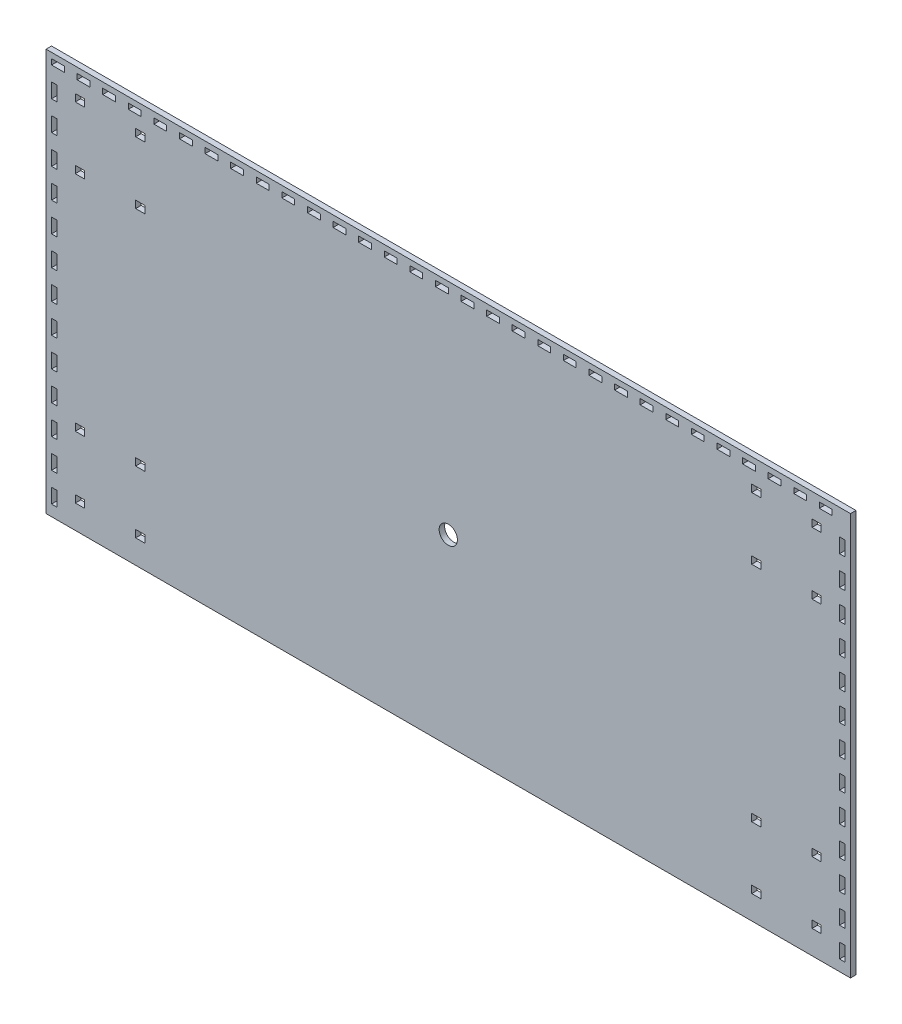
SolidWorks part; units mm, degrees
ref_plane "Plan de face" through (0, 0, 0) normal (0, 0, 1) x (1, 0, 0)
ref_plane "Plan de dessus" through (0, 0, 0) normal (0, 1, 0) x (1, 0, 0)
ref_plane "Plan de droite" through (0, 0, 0) normal (1, 0, 0) x (0, 0, -1)
sketch "Esquisse1" plane through (0, 0, 0) normal (0, 0, 1) x (1, 0, 0)
  line L1 (-220, 110) -> (220, 110)
  line L2 (-220, 110) -> (-220, -110)
  line L3 (-220, -110) -> (220, -110)
  line L4 (220, 110) -> (220, -110)
  line L5 (-220, 110) -> (220, -110) construction
  line L6 (-220, -110) -> (220, 110) construction
  point P0 (0, 0)
  dimension "D1" = 440
  dimension "D2" = 220
extrude "Boss.-Extru.1" add sketch "Esquisse1" along normal blind 3
sketch "Esquisse2" plane through (0, 0, 3) normal (0, 0, 1) x (1, 0, 0)
  line L0 (-220, -10) -> (220, -10) construction
  line L1 (-220, 110) -> (-220, -110) construction
  line L2 (220, -110) -> (220, 110) construction
  line L3 (0, 110) -> (0, -110) construction
  line L4 (220, 110) -> (-220, 110) construction
  line L5 (-220, -110) -> (220, -110) construction
  circle A0 centre (0, -10) radius 5
  dimension "D2" = 10
  dimension "D1" = 100
extrude "Enlèv. mat.-Extru.1" cut sketch "Esquisse2" against normal blind 3
sketch "Esquisse3" plane through (0, 0, 3) normal (0, 0, 1) x (1, 0, 0)
  line L0 (-185, 94) -> (-185, 62) construction
  line L1 (-201, 78) -> (-169, 78) construction
  line L2 (-220, 110) -> (-220, -110) construction
  line L3 (220, 110) -> (-220, 110) construction
  line L4 (-171, 95) -> (-199, 95) construction
  line L5 (-204, 97) -> (-199, 97)
  line L6 (-204, 97) -> (-204, 93)
  line L7 (-204, 93) -> (-199, 93)
  line L8 (-199, 97) -> (-199, 93)
  line L9 (-204, 97) -> (-199, 93) construction
  line L10 (-204, 93) -> (-199, 97) construction
  line L11 (-166, 97) -> (-171, 97)
  line L12 (-166, 97) -> (-166, 93)
  line L13 (-166, 93) -> (-171, 93)
  line L14 (-171, 97) -> (-171, 93)
  line L15 (-166, 97) -> (-171, 93) construction
  line L16 (-166, 93) -> (-171, 97) construction
  line L17 (-166, 63) -> (-171, 63)
  line L18 (-166, 59) -> (-166, 63)
  line L19 (-166, 59) -> (-171, 59)
  line L20 (-171, 59) -> (-171, 63)
  line L21 (-199, 59) -> (-199, 63)
  line L22 (-204, 63) -> (-199, 63)
  line L23 (-204, 59) -> (-204, 63)
  line L24 (-204, 59) -> (-199, 59)
  line L25 (0, 110) -> (0, -110) construction
  line L26 (-220, -110) -> (220, -110) construction
  line L27 (-220, 0) -> (220, 0) construction
  line L28 (220, -110) -> (220, 110) construction
  line L29 (171, 59) -> (171, 63)
  line L30 (166, 59) -> (171, 59)
  line L31 (166, 59) -> (166, 63)
  line L32 (166, 63) -> (171, 63)
  line L33 (204, 59) -> (199, 59)
  line L34 (204, 59) -> (204, 63)
  line L35 (204, 63) -> (199, 63)
  line L36 (199, 59) -> (199, 63)
  line L37 (166, 93) -> (171, 93)
  line L38 (166, 97) -> (166, 93)
  line L39 (166, 97) -> (171, 97)
  line L40 (171, 97) -> (171, 93)
  line L41 (199, 97) -> (199, 93)
  line L42 (204, 93) -> (199, 93)
  line L43 (204, 97) -> (204, 93)
  line L44 (204, 97) -> (199, 97)
  line L45 (-166, -97) -> (-166, -93)
  line L46 (-166, -93) -> (-171, -93)
  line L47 (-171, -97) -> (-171, -93)
  line L48 (-166, -97) -> (-171, -97)
  line L49 (-204, -93) -> (-199, -93)
  line L50 (-199, -97) -> (-199, -93)
  line L51 (-204, -97) -> (-199, -97)
  line L52 (-204, -97) -> (-204, -93)
  line L53 (-166, -63) -> (-171, -63)
  line L54 (-171, -59) -> (-171, -63)
  line L55 (-166, -59) -> (-171, -59)
  line L56 (-166, -59) -> (-166, -63)
  line L57 (-204, -59) -> (-199, -59)
  line L58 (-204, -59) -> (-204, -63)
  line L59 (-204, -63) -> (-199, -63)
  line L60 (-199, -59) -> (-199, -63)
  line L61 (204, -97) -> (199, -97)
  line L62 (204, -97) -> (204, -93)
  line L63 (204, -93) -> (199, -93)
  line L64 (199, -97) -> (199, -93)
  line L65 (171, -97) -> (171, -93)
  line L66 (166, -97) -> (171, -97)
  line L67 (166, -97) -> (166, -93)
  line L68 (166, -93) -> (171, -93)
  line L69 (199, -59) -> (199, -63)
  line L70 (204, -63) -> (199, -63)
  line L71 (204, -59) -> (204, -63)
  line L72 (204, -59) -> (199, -59)
  line L73 (166, -63) -> (171, -63)
  line L74 (166, -59) -> (166, -63)
  line L75 (166, -59) -> (171, -59)
  line L76 (171, -59) -> (171, -63)
  circle A0 centre (-185, 78) radius 16 construction
  point P10 (-201.5, 95)
  point P15 (-168.5, 95)
  dimension "D1" = 35
  dimension "D3" = 32
  dimension "D2" = 32
  dimension "D4" = 5
  dimension "D5" = 4
  dimension "D6" = 28
  dimension "D7" = 5
  dimension "D8" = 4
  dimension "D9" = 15
  dimension "D10" = 14
extrude "Enlèv. mat.-Extru.2" cut sketch "Esquisse3" against normal blind 3
sketch "Esquisse4" plane through (0, 0, 3) normal (0, 0, 1) x (1, 0, 0)
  line L0 (220, 110) -> (-220, 110) construction
  line L1 (-217, 107) -> (-210, 107)
  line L2 (-217, 107) -> (-217, 104)
  line L3 (-217, 104) -> (-210, 104)
  line L4 (-210, 107) -> (-210, 104)
  line L5 (-220, 110) -> (-220, -110) construction
  line L6 (-203, 107) -> (-203, 104)
  line L7 (-203, 107) -> (-196, 107)
  line L8 (-196, 107) -> (-196, 104)
  line L9 (-203, 104) -> (-196, 104)
  line L10 (-189, 107) -> (-189, 104)
  line L11 (-189, 107) -> (-182, 107)
  line L12 (-182, 107) -> (-182, 104)
  line L13 (-189, 104) -> (-182, 104)
  line L14 (-175, 107) -> (-175, 104)
  line L15 (-175, 107) -> (-168, 107)
  line L16 (-168, 107) -> (-168, 104)
  line L17 (-175, 104) -> (-168, 104)
  line L18 (-161, 107) -> (-161, 104)
  line L19 (-161, 107) -> (-154, 107)
  line L20 (-154, 107) -> (-154, 104)
  line L21 (-161, 104) -> (-154, 104)
  line L22 (-147, 107) -> (-147, 104)
  line L23 (-147, 107) -> (-140, 107)
  line L24 (-140, 107) -> (-140, 104)
  line L25 (-147, 104) -> (-140, 104)
  line L26 (-133, 107) -> (-133, 104)
  line L27 (-133, 107) -> (-126, 107)
  line L28 (-126, 107) -> (-126, 104)
  line L29 (-133, 104) -> (-126, 104)
  line L30 (-119, 107) -> (-119, 104)
  line L31 (-119, 107) -> (-112, 107)
  line L32 (-112, 107) -> (-112, 104)
  line L33 (-119, 104) -> (-112, 104)
  line L34 (-105, 107) -> (-105, 104)
  line L35 (-105, 107) -> (-98, 107)
  line L36 (-98, 107) -> (-98, 104)
  line L37 (-105, 104) -> (-98, 104)
  line L38 (-91, 107) -> (-91, 104)
  line L39 (-91, 107) -> (-84, 107)
  line L40 (-84, 107) -> (-84, 104)
  line L41 (-91, 104) -> (-84, 104)
  line L42 (-77, 107) -> (-77, 104)
  line L43 (-77, 107) -> (-70, 107)
  line L44 (-70, 107) -> (-70, 104)
  line L45 (-77, 104) -> (-70, 104)
  line L46 (-63, 107) -> (-63, 104)
  line L47 (-63, 107) -> (-56, 107)
  line L48 (-56, 107) -> (-56, 104)
  line L49 (-63, 104) -> (-56, 104)
  line L50 (-49, 107) -> (-49, 104)
  line L51 (-49, 107) -> (-42, 107)
  line L52 (-42, 107) -> (-42, 104)
  line L53 (-49, 104) -> (-42, 104)
  line L54 (-35, 107) -> (-35, 104)
  line L55 (-35, 107) -> (-28, 107)
  line L56 (-28, 107) -> (-28, 104)
  line L57 (-35, 104) -> (-28, 104)
  line L58 (-21, 107) -> (-21, 104)
  line L59 (-21, 107) -> (-14, 107)
  line L60 (-14, 107) -> (-14, 104)
  line L61 (-21, 104) -> (-14, 104)
  line L62 (-7, 107) -> (-7, 104)
  line L63 (-7, 107) -> (0, 107)
  line L64 (0, 107) -> (0, 104)
  line L65 (-7, 104) -> (0, 104)
  line L66 (7, 107) -> (7, 104)
  line L67 (7, 107) -> (14, 107)
  line L68 (14, 107) -> (14, 104)
  line L69 (7, 104) -> (14, 104)
  line L70 (21, 107) -> (21, 104)
  line L71 (21, 107) -> (28, 107)
  line L72 (28, 107) -> (28, 104)
  line L73 (21, 104) -> (28, 104)
  line L74 (35, 107) -> (35, 104)
  line L75 (35, 107) -> (42, 107)
  line L76 (42, 107) -> (42, 104)
  line L77 (35, 104) -> (42, 104)
  line L78 (49, 107) -> (49, 104)
  line L79 (49, 107) -> (56, 107)
  line L80 (56, 107) -> (56, 104)
  line L81 (49, 104) -> (56, 104)
  line L82 (63, 107) -> (63, 104)
  line L83 (63, 107) -> (70, 107)
  line L84 (70, 107) -> (70, 104)
  line L85 (63, 104) -> (70, 104)
  line L86 (77, 107) -> (77, 104)
  line L87 (77, 107) -> (84, 107)
  line L88 (84, 107) -> (84, 104)
  line L89 (77, 104) -> (84, 104)
  line L90 (91, 107) -> (91, 104)
  line L91 (91, 107) -> (98, 107)
  line L92 (98, 107) -> (98, 104)
  line L93 (91, 104) -> (98, 104)
  line L94 (105, 107) -> (105, 104)
  line L95 (105, 107) -> (112, 107)
  line L96 (112, 107) -> (112, 104)
  line L97 (105, 104) -> (112, 104)
  line L98 (119, 107) -> (119, 104)
  line L99 (119, 107) -> (126, 107)
  line L100 (126, 107) -> (126, 104)
  line L101 (119, 104) -> (126, 104)
  line L102 (133, 107) -> (133, 104)
  line L103 (133, 107) -> (140, 107)
  line L104 (140, 107) -> (140, 104)
  line L105 (133, 104) -> (140, 104)
  line L106 (147, 107) -> (147, 104)
  line L107 (147, 107) -> (154, 107)
  line L108 (154, 107) -> (154, 104)
  line L109 (147, 104) -> (154, 104)
  line L110 (161, 107) -> (161, 104)
  line L111 (161, 107) -> (168, 107)
  line L112 (168, 107) -> (168, 104)
  line L113 (161, 104) -> (168, 104)
  line L114 (175, 107) -> (175, 104)
  line L115 (175, 107) -> (182, 107)
  line L116 (182, 107) -> (182, 104)
  line L117 (175, 104) -> (182, 104)
  line L118 (189, 107) -> (189, 104)
  line L119 (189, 107) -> (196, 107)
  line L120 (196, 107) -> (196, 104)
  line L121 (189, 104) -> (196, 104)
  line L122 (203, 107) -> (203, 104)
  line L123 (203, 107) -> (210, 107)
  line L124 (210, 107) -> (210, 104)
  line L125 (203, 104) -> (210, 104)
  dimension "D1" = 7
  dimension "D2" = 3
  dimension "D3" = 3
  dimension "D4" = 3
  dimension "D6" = 7
  dimension "D5" = 31
extrude "Enlèv. mat.-Extru.3" cut sketch "Esquisse4" against normal blind 3
sketch "Esquisse5" plane through (0, 0, 3) normal (0, 0, 1) x (1, 0, 0)
  line L0 (-220, -110) -> (220, -110) construction
  line L1 (-217, -104) -> (-214, -104)
  line L2 (-217, -104) -> (-217, -96)
  line L3 (-217, -96) -> (-214, -96)
  line L4 (-214, -104) -> (-214, -96)
  line L5 (-220, 110) -> (-220, -110) construction
  line L6 (-217, -80) -> (-214, -80)
  line L7 (-217, -88) -> (-217, -80)
  line L8 (-214, -88) -> (-214, -80)
  line L9 (-217, -88) -> (-214, -88)
  line L10 (-217, -64) -> (-214, -64)
  line L11 (-217, -72) -> (-217, -64)
  line L12 (-214, -72) -> (-214, -64)
  line L13 (-217, -72) -> (-214, -72)
  line L14 (-217, -48) -> (-214, -48)
  line L15 (-217, -56) -> (-217, -48)
  line L16 (-214, -56) -> (-214, -48)
  line L17 (-217, -56) -> (-214, -56)
  line L18 (-217, -32) -> (-214, -32)
  line L19 (-217, -40) -> (-217, -32)
  line L20 (-214, -40) -> (-214, -32)
  line L21 (-217, -40) -> (-214, -40)
  line L22 (-217, -16) -> (-214, -16)
  line L23 (-217, -24) -> (-217, -16)
  line L24 (-214, -24) -> (-214, -16)
  line L25 (-217, -24) -> (-214, -24)
  line L26 (-217, 0) -> (-214, 0)
  line L27 (-217, -8) -> (-217, 0)
  line L28 (-214, -8) -> (-214, 0)
  line L29 (-217, -8) -> (-214, -8)
  line L30 (-217, 16) -> (-214, 16)
  line L31 (-217, 8) -> (-217, 16)
  line L32 (-214, 8) -> (-214, 16)
  line L33 (-217, 8) -> (-214, 8)
  line L34 (-217, 32) -> (-214, 32)
  line L35 (-217, 24) -> (-217, 32)
  line L36 (-214, 24) -> (-214, 32)
  line L37 (-217, 24) -> (-214, 24)
  line L38 (-217, 48) -> (-214, 48)
  line L39 (-217, 40) -> (-217, 48)
  line L40 (-214, 40) -> (-214, 48)
  line L41 (-217, 40) -> (-214, 40)
  line L42 (-217, 64) -> (-214, 64)
  line L43 (-217, 56) -> (-217, 64)
  line L44 (-214, 56) -> (-214, 64)
  line L45 (-217, 56) -> (-214, 56)
  line L46 (-217, 80) -> (-214, 80)
  line L47 (-217, 72) -> (-217, 80)
  line L48 (-214, 72) -> (-214, 80)
  line L49 (-217, 72) -> (-214, 72)
  line L50 (-217, 96) -> (-214, 96)
  line L51 (-217, 88) -> (-217, 96)
  line L52 (-214, 88) -> (-214, 96)
  line L53 (-217, 88) -> (-214, 88)
  line L54 (0, 110) -> (0, -110) construction
  line L55 (220, 110) -> (-220, 110) construction
  line L56 (217, 88) -> (214, 88)
  line L57 (214, 88) -> (214, 96)
  line L58 (217, 88) -> (217, 96)
  line L59 (217, 96) -> (214, 96)
  line L60 (217, 72) -> (214, 72)
  line L61 (214, 72) -> (214, 80)
  line L62 (217, 72) -> (217, 80)
  line L63 (217, 80) -> (214, 80)
  line L64 (217, 56) -> (214, 56)
  line L65 (214, 56) -> (214, 64)
  line L66 (217, 56) -> (217, 64)
  line L67 (217, 64) -> (214, 64)
  line L68 (217, 40) -> (214, 40)
  line L69 (214, 40) -> (214, 48)
  line L70 (217, 40) -> (217, 48)
  line L71 (217, 48) -> (214, 48)
  line L72 (217, 24) -> (214, 24)
  line L73 (214, 24) -> (214, 32)
  line L74 (217, 24) -> (217, 32)
  line L75 (217, 32) -> (214, 32)
  line L76 (217, 8) -> (214, 8)
  line L77 (214, 8) -> (214, 16)
  line L78 (217, 8) -> (217, 16)
  line L79 (217, 16) -> (214, 16)
  line L80 (217, -8) -> (214, -8)
  line L81 (214, -8) -> (214, 0)
  line L82 (217, -8) -> (217, 0)
  line L83 (217, 0) -> (214, 0)
  line L84 (217, -24) -> (214, -24)
  line L85 (214, -24) -> (214, -16)
  line L86 (217, -24) -> (217, -16)
  line L87 (217, -16) -> (214, -16)
  line L88 (217, -40) -> (214, -40)
  line L89 (214, -40) -> (214, -32)
  line L90 (217, -40) -> (217, -32)
  line L91 (217, -32) -> (214, -32)
  line L92 (217, -56) -> (214, -56)
  line L93 (214, -56) -> (214, -48)
  line L94 (217, -56) -> (217, -48)
  line L95 (217, -48) -> (214, -48)
  line L96 (217, -72) -> (214, -72)
  line L97 (214, -72) -> (214, -64)
  line L98 (217, -72) -> (217, -64)
  line L99 (217, -64) -> (214, -64)
  line L100 (217, -88) -> (214, -88)
  line L101 (214, -88) -> (214, -80)
  line L102 (217, -88) -> (217, -80)
  line L103 (217, -80) -> (214, -80)
  line L104 (214, -104) -> (214, -96)
  line L105 (217, -96) -> (214, -96)
  line L106 (217, -104) -> (217, -96)
  line L107 (217, -104) -> (214, -104)
  dimension "D1" = 8
  dimension "D2" = 3
  dimension "D3" = 6
  dimension "D4" = 3
  dimension "D6" = 8
  dimension "D5" = 13
extrude "Enlèv. mat.-Extru.4" cut sketch "Esquisse5" against normal blind 3
